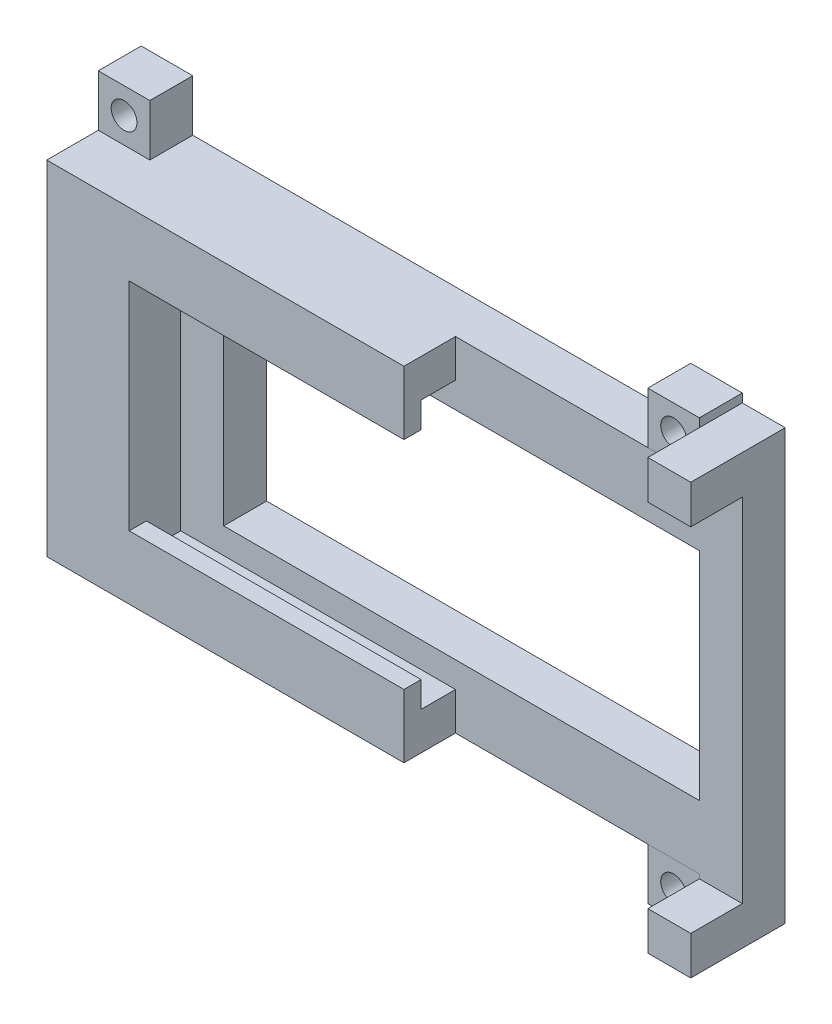
SolidWorks part; units mm, degrees
ref_plane "Front Plane" through (0, 0, 0) normal (1, 0, 0) x (0, 1, 0)
ref_plane "Top Plane" through (0, 0, 0) normal (0, 0, 1) x (0, 1, 0)
ref_plane "Right Plane" through (0, 0, 0) normal (0, 1, 0) x (-1, 0, 0)
sketch "Sketch1" plane through (0, 0, 0) normal (0, 0, 1) x (0, 1, 0)
  line L2 (-20, 5) -> (-20, 75)
  line L3 (-20, 75) -> (20, 75)
  line L4 (20, 5) -> (20, 75)
  line L5 (-25, 0) -> (-25, 5)
  line L6 (-25, 5) -> (-20, 5)
  line L7 (0, 75) -> (0, 0) construction
  line L9 (25, 0) -> (25, 5)
  line L10 (25, 5) -> (20, 5)
  line L11 (-25, 0) -> (25, 0)
  dimension "D1" = 40
  dimension "D2" = 5
  dimension "D3" = 5
  dimension "D4" = 75
extrude "Boss-Extrude1" add sketch "Sketch1" along normal blind 5
sketch "Sketch4" plane through (0, 0, 5) normal (0, 0, 1) x (1, 0, 0)
  line L0 (-75, 20) -> (-75, -20)
  line L1 (-5, 20.5) -> (0, 20.5)
  line L2 (-5, 20.5) -> (-5, 25)
  line L3 (-5, 25) -> (0, 25)
  line L4 (0, 20.5) -> (0, 25)
  line L9 (-75, 20) -> (-33.4, 20)
  line L11 (-65.4, 15.6) -> (-33.4, 15.6)
  line L12 (-33.4, 20) -> (-33.4, 15.6)
  line L13 (-75, -20) -> (-33.4, -20)
  line L15 (-65.4, -15.6) -> (-33.4, -15.6)
  line L16 (-33.4, -20) -> (-33.4, -15.6)
  line L17 (-65.4, 15.6) -> (-65.4, -15.6)
  line L18 (-5, 20) -> (-75, 20) construction
  line L19 (-5, 25) -> (-5, 20) construction
  line L20 (0, 0) -> (-65.4, 0) construction
  line L21 (-5, -25) -> (0, -25)
  line L22 (0, -20.5) -> (0, -25)
  line L23 (-5, -20.5) -> (0, -20.5)
  line L24 (-5, -20.5) -> (-5, -25)
  dimension "D1" = 4.4
  dimension "D2" = 32
  dimension "D3" = 4.4
  dimension "D4" = 9.6
  dimension "D5" = 0.5
extrude "Boss-Extrude2" add sketch "Sketch4" along normal blind 6
sketch "Sketch5" plane through (-65.4, 0, 0) normal (1, 0, 0) x (0, 1, 0)
  line L0 (0, 11) -> (0, 5) construction
  line L1 (-15.6, 11) -> (-12.6, 11)
  line L2 (-15.6, 11) -> (-15.6, 9)
  line L3 (-15.6, 9) -> (-12.6, 9)
  line L4 (-12.6, 11) -> (-12.6, 9)
  line L5 (-15.6, 11) -> (15.6, 11) construction
  line L6 (-15.6, 5) -> (15.6, 5) construction
  line L7 (15.6, 9) -> (12.6, 9)
  line L8 (12.6, 11) -> (12.6, 9)
  line L9 (15.6, 11) -> (12.6, 11)
  line L10 (15.6, 11) -> (15.6, 9)
  dimension "D1" = 3
  dimension "D2" = 2
extrude "Boss-Extrude3" add sketch "Sketch5" along normal up to surface (32 mm away) up to face at (-33.4, -17.8, 8)
sketch "Sketch6" plane through (0, 0, 0) normal (0, 0, -1) x (1, 0, 0)
  line L0 (-40, 20) -> (-40, -20) construction
  line L1 (-5, 20) -> (-11, 20)
  line L2 (-5, 20) -> (-5, 26)
  line L3 (-5, 26) -> (-11, 26)
  line L4 (-11, 20) -> (-11, 26)
  line L5 (-75, 20) -> (-5, 20) construction
  line L6 (-5, -20) -> (-75, -20) construction
  line L7 (-75, 0) -> (0, 0) construction
  line L8 (-75, -20) -> (-75, 20) construction
  line L9 (-75, 26) -> (-69, 26)
  line L10 (-69, 20) -> (-69, 26)
  line L11 (-75, 20) -> (-69, 20)
  line L12 (-75, 20) -> (-75, 26)
  line L13 (-5, -26) -> (-11, -26)
  line L14 (-11, -20) -> (-11, -26)
  line L15 (-5, -20) -> (-11, -20)
  line L16 (-5, -20) -> (-5, -26)
  line L17 (-75, -20) -> (-75, -26)
  line L18 (-75, -20) -> (-69, -20)
  line L19 (-69, -20) -> (-69, -26)
  line L20 (-75, -26) -> (-69, -26)
  dimension "D1" = 6
extrude "Boss-Extrude4" add sketch "Sketch6" against normal blind 5 separate body
sketch "Sketch7" plane through (0, 0, 5) normal (0, 0, 1) x (1, 0, 0)
  line L0 (-11, -23) -> (-5, -23) construction
  line L1 (-11, -26) -> (-11, -20) construction
  line L2 (-5, -20) -> (-5, -26) construction
  line L3 (0, 0) -> (-65.4, 0) construction
  line L4 (-65.4, -15.6) -> (-65.4, 15.6) construction
  line L5 (-75, -23) -> (-69, -23) construction
  line L6 (-75, -26) -> (-75, -20) construction
  line L7 (-69, -20) -> (-69, -26) construction
  circle A0 centre (-8, -23) radius 1.5
  circle A1 centre (-72, -23) radius 1.5
  circle A2 centre (-8, 23) radius 1.5
  circle A3 centre (-72, 23) radius 1.5
  dimension "D1" = 3
  dimension "D2" = 3
extrude "Cut-Extrude1" cut sketch "Sketch7" against normal through all
sketch "Sketch8" plane through (0, 0, 5) normal (0, 0, 1) x (1, 0, 0)
  line L1 (-60.4, -12.6) -> (-5, -12.6)
  line L2 (-60.4, -12.6) -> (-60.4, 12.6)
  line L3 (-60.4, 12.6) -> (-5, 12.6)
  line L4 (-5, -12.6) -> (-5, 12.6)
  line L6 (-65.4, -15.6) -> (-65.4, 15.6) construction
  line L7 (-33.4, 12.6) -> (-65.4, 12.6) construction
  line L8 (-33.4, -12.6) -> (-65.4, -12.6) construction
  line L9 (0, -20.5) -> (0, 20.5) construction
  dimension "D1" = 5
  dimension "D2" = 5
extrude "Cut-Extrude2" cut sketch "Sketch8" against normal through all
